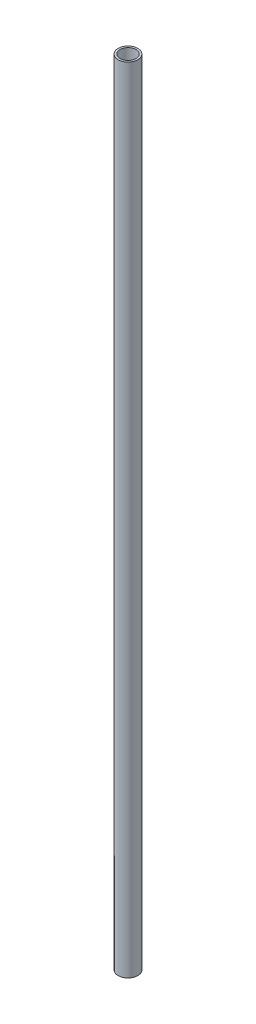
SolidWorks part; units mm, degrees
ref_plane "Front Plane" through (0, 0, 0) normal (0, 0, 1) x (1, 0, 0)
ref_plane "Top Plane" through (0, 0, 0) normal (0, 1, 0) x (1, 0, 0)
ref_plane "Right Plane" through (0, 0, 0) normal (1, 0, 0) x (0, 0, -1)
sketch "Sketch1" plane through (0, 0, 0) normal (0, 1, 0) x (1, 0, 0)
  circle A0 centre (0, 0) radius 0.25
  circle A1 centre (0, 0) radius 0.31
extrude "Boss-Extrude1" add sketch "Sketch1" along normal blind 25
